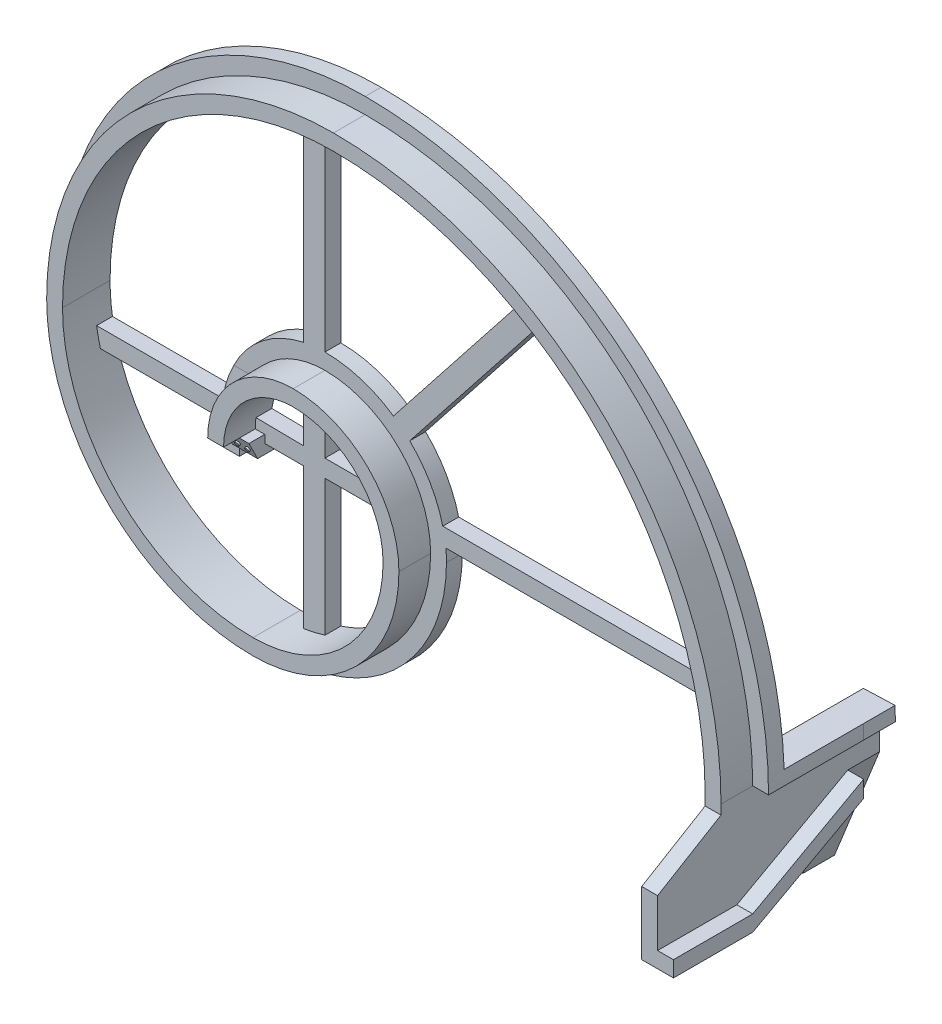
SolidWorks part; units mm, degrees
ref_plane "Front" through (0, 0, 0) normal (0, 0, 1) x (1, 0, 0)
ref_plane "Top" through (0, 0, 0) normal (0, 1, 0) x (1, 0, 0)
ref_plane "Right" through (0, 0, 0) normal (1, 0, 0) x (0, 0, -1)
sketch "Sketch2" plane through (0, 0, 0) normal (0, 0, 1) x (1, 0, 0)
  line L0 (-26.9875, 0) -> (-26.9875, -10)
  line L1 (129.9375, -19.05) -> (134.9375, -19.05)
  line L2 (-21.9875, 0) -> (-21.9875, -10)
  line L3 (-26.9875, -10) -> (-21.9875, -10)
  arc A0 (-21.9875, 0) -> (0, 21.9875) centre (0, 0) cw
  arc A1 (0, 21.9875) -> (28.3375, -6.35) centre (0, -6.35) cw
  arc A2 (28.3375, -6.35) -> (-12.7, -47.3875) centre (-12.7, -6.35) cw
  arc A3 (-12.7, -47.3875) -> (-72.7875, 12.7) centre (-12.7, 12.7) cw
  arc A4 (-72.7875, 12.7) -> (12.7, 98.1875) centre (12.7, 12.7) cw
  arc A5 (12.7, 98.1875) -> (129.9375, -19.05) centre (12.7, -19.05) cw
  arc A6 (-26.9875, 0) -> (0, 26.9875) centre (0, 0) cw
  arc A7 (0, 26.9875) -> (33.3375, -6.35) centre (0, -6.35) cw
  arc A8 (33.3375, -6.35) -> (-12.7, -52.3875) centre (-12.7, -6.35) cw
  arc A9 (-12.7, -52.3875) -> (-77.7875, 12.7) centre (-12.7, 12.7) cw
  arc A10 (-77.7875, 12.7) -> (12.7, 103.1875) centre (12.7, 12.7) cw
  arc A11 (12.7, 103.1875) -> (134.9375, -19.05) centre (12.7, -19.05) cw
extrude "Extrude2" add sketch "Sketch2" along normal blind 10
sketch "Sketch3" plane through (0, 0, 0) normal (0, 0, 1) x (1, 0, 0)
  line L0 (-21.9875, 0) -> (-21.9875, -10)
  line L1 (129.9375, -19.05) -> (139.9375, -19.05)
  line L2 (-21.9875, -10) -> (-31.9875, -10)
  line L3 (-31.9875, -10) -> (-31.9875, 0)
  arc A0 (0, 21.9875) -> (-21.9875, 0) centre (0, 0) ccw
  arc A1 (0, 31.9875) -> (-31.9875, 0) centre (0, 0) ccw
  arc A2 (0, 21.9875) -> (28.3375, -6.35) centre (0, -6.35) cw
  arc A3 (0, 31.9875) -> (38.3375, -6.35) centre (0, -6.35) cw
  arc A4 (28.3375, -6.35) -> (-12.7, -47.3875) centre (-12.7, -6.35) cw
  arc A5 (38.3375, -6.35) -> (-12.7, -57.3875) centre (-12.7, -6.35) cw
  arc A6 (-12.7, -47.3875) -> (-72.7875, 12.7) centre (-12.7, 12.7) cw
  arc A7 (-12.7, -57.3875) -> (-82.7875, 12.7) centre (-12.7, 12.7) cw
  arc A8 (-72.7875, 12.7) -> (12.7, 98.1875) centre (12.7, 12.7) cw
  arc A9 (-82.7875, 12.7) -> (12.7, 108.1875) centre (12.7, 12.7) cw
  arc A10 (12.7, 98.1875) -> (129.9375, -19.05) centre (12.7, -19.05) cw
  arc A11 (12.7, 108.1875) -> (139.9375, -19.05) centre (12.7, -19.05) cw
extrude "Extrude3" add sketch "Sketch3" against normal blind 5
sketch "Sketch4" plane through (-26.9875, 0, 0) normal (-1, 0, 0) x (0, 0, 1)
  line L0 (0, -10) -> (5, 0)
  line L1 (10, -10) -> (0, -10) construction
  line L4 (10, 0) -> (-5, 0) construction
  line L5 (10, -10) -> (0, -10)
  line L6 (5, 0) -> (10, 0)
  line L7 (10, 0) -> (10, -10)
extrude "Cut-Extrude1" cut sketch "Sketch4" against normal blind 5
sketch "Sketch5" plane through (-21.9875, 0, 0) normal (1, 0, 0) x (0, 0, -1)
  line L0 (0, -10) -> (-5, 0)
  line L1 (-5, 0) -> (0, 0)
  line L2 (0, -10) -> (5, -10)
  line L3 (5, -10) -> (5, 0)
  line L4 (5, 0) -> (0, 0)
extrude "Extrude4" add sketch "Sketch5" along normal blind 3
sketch "Sketch6" plane through (-18.9875, 0, 0) normal (1, 0, 0) x (0, 0, -1)
  line L0 (5, -5.5) -> (-2.25, -5.5)
  line L1 (5, -19.05) -> (5, 108.1875) construction
  line L2 (-5, 0) -> (0, -10) construction
  line L3 (-2.25, -5.5) -> (0, -10)
  line L4 (0, -10) -> (5, -10)
  line L5 (5, -10) -> (5, -5.5)
extrude "Cut-Extrude2" cut sketch "Sketch6" against normal blind 8
sketch "Sketch7" plane through (-26.9875, 0, 0) normal (-1, 0, 0) x (0, 0, 1)
  line L0 (0, -5.5) -> (0.7981, -5.5)
  line L1 (0.7981, -5.5) -> (0, 14)
  line L2 (0, 14) -> (0, -5.5)
extrude "Extrude5" add sketch "Sketch7" along normal blind 5 and the other way blind 5
sketch "Sketch8" plane through (0, 0, 0) normal (0, 0, 1) x (1, 0, 0)
  line L0 (-28.7611, 14) -> (-31.9875, 14)
  line L1 (-31.9875, 14) -> (-31.9875, 0)
  arc A0 (-31.9875, 0) -> (-28.7611, 14) centre (0, 0) cw
extrude "Cut-Extrude3" cut sketch "Sketch8" along normal blind 5
sketch "Sketch9" plane through (0, -19.05, 0) normal (0, -1, 0) x (1, 0, 0)
  line L0 (129.9375, 10) -> (129.9375, -5)
  line L1 (129.9375, -5) -> (134.9375, -5)
  line L2 (129.9375, -5) -> (139.9375, -5) construction
  line L3 (134.9375, -5) -> (134.9375, 10)
  line L4 (134.9375, 10) -> (129.9375, 10)
extrude "Extrude6" add sketch "Sketch9" along normal blind 35
sketch "Sketch11" plane through (0, 0, -5) normal (0, 0, -1) x (-1, 0, 0)
  line L0 (-134.9375, -19.05) -> (-129.9375, -19.05)
  line L1 (-129.9375, -19.05) -> (-129.9375, -54.05)
  line L2 (-129.9375, -54.05) -> (-134.9375, -54.05)
  line L3 (-134.9375, -54.05) -> (-134.9375, -19.05)
extrude "Extrude8" add sketch "Sketch11" along normal blind 25
sketch "Sketch12" plane through (0, 0, -5) normal (0, 0, -1) x (-1, 0, 0)
  line L0 (-129.9375, -19.05) -> (-139.9375, -19.05)
  line L1 (-129.8661, -14.9585) -> (-139.86, -14.6095)
  arc A0 (-129.9375, -19.05) -> (-129.8661, -14.9585) centre (-12.7, -19.05) cw
  arc A1 (-139.9375, -19.05) -> (-139.86, -14.6095) centre (-12.7, -19.05) cw
extrude "Extrude9" add sketch "Sketch12" along normal blind 25
sketch "Sketch16" plane through (0, 0, 10) normal (0, 0, 1) x (1, 0, 0)
  line L0 (129.9375, -19.05) -> (129.9375, -54.05)
  line L1 (129.9375, -54.05) -> (139.9375, -54.05)
  line L2 (139.9375, -54.05) -> (139.9375, -49.05)
  line L3 (139.9375, -49.05) -> (134.9375, -49.05)
  line L4 (134.9375, -54.05) -> (134.9375, -19.05) construction
  line L5 (134.9375, -49.05) -> (134.9375, -19.05)
  line L6 (134.9375, -19.05) -> (129.9375, -19.05)
extrude "Extrude12" add sketch "Sketch16" along normal blind 20
sketch "Sketch17" plane through (134.9375, 0, 0) normal (1, 0, 0) x (0, 0, -1)
  line L0 (-10, -54.05) -> (-10, -49.05)
  line L1 (-10, -49.05) -> (-5, -49.05)
  line L2 (-5, -49.05) -> (30, -29.7287)
  line L3 (-10, -54.05) -> (-5, -54.05)
  line L4 (30, -54.05) -> (-10, -54.05) construction
  line L5 (-5, -54.05) -> (30, -34.9887)
  line L6 (30, -19.05) -> (30, -54.05) construction
  line L7 (30, -34.9887) -> (30, -29.7287)
extrude "Extrude13" add sketch "Sketch17" along normal blind 5
sketch "Sketch18" plane through (134.9375, 0, 0) normal (1, 0, 0) x (0, 0, -1)
  line L0 (-5, -54.05) -> (30, -34.9887)
  line L1 (30, -34.9887) -> (30, -54.05)
  line L2 (30, -54.05) -> (-5, -54.05)
  line L4 (-30, -49.05) -> (-30, -19.05) construction
  line L6 (-30, -19.05) -> (-30, -34.05)
  line L7 (-30, -19.05) -> (-10, -19.05)
  line L8 (-10, -19.05) -> (-10, -22.05)
  line L9 (-10, -22.05) -> (-30, -34.05)
extrude "Cut-Extrude5" cut sketch "Sketch18" against normal blind 5
sketch "Sketch19" plane through (0, 0, -30) normal (0, 0, -1) x (-1, 0, 0)
  line L0 (-134.9375, -19.05) -> (-134.9375, -29.7287)
  line L1 (-134.9375, -29.7287) -> (-120.74, -65.09)
  line L2 (-120.74, -65.09) -> (-115.74, -65.09)
  line L3 (-115.74, -65.09) -> (-129.9375, -29.7287)
  line L4 (-129.9375, -34.9887) -> (-129.9375, -19.05) construction
  line L5 (-129.9375, -29.7287) -> (-129.8661, -14.9585)
  line L6 (-129.8661, -14.9585) -> (-139.86, -14.6095)
  line L7 (-139.86, -14.6095) -> (-139.9375, -19.05)
  line L8 (-139.9375, -19.05) -> (-134.9375, -19.05)
extrude "Extrude14" add sketch "Sketch19" along normal blind 10
sketch "Sketch20" plane through (0, 0, 0) normal (0, 0, 1) x (1, 0, 0)
  line L0 (128.7609, -2.482) -> (38.1419, -2.482)
  line L1 (0, 31.9875) -> (0, 97.2389)
  line L2 (37.1788, 3.004) -> (127.8445, 3.004)
  line L3 (-6.7456, 31.2682) -> (-6.7456, 95.9465)
  line L4 (-0.0007, 21.9875) -> (-0.0007, 3.004)
  line L5 (-0.0007, 3.004) -> (26.7491, 3.004)
  line L6 (28.0723, -2.482) -> (0.0805, -2.482)
  line L7 (0.0805, -2.482) -> (0.0805, -45.3123)
  line L8 (-6.7456, 20.9272) -> (-6.7456, 3.004)
  line L9 (-6.7456, 3.004) -> (-21.7528, 3.2043)
  line L10 (-21.9875, 0) -> (-18.9875, 0)
  line L11 (-18.9875, 0) -> (-18.9875, -2.482)
  line L12 (-18.9875, -2.482) -> (-6.7456, -2.482)
  line L13 (-6.7456, -2.482) -> (-6.7456, -46.92)
  line L14 (-31.8266, 3.2043) -> (-50.9222, 3.2043)
  line L15 (-31.9875, 0) -> (-31.9875, -2.4841)
  line L16 (-31.9875, -5.5) -> (-31.9875, 0) construction
  line L17 (-50.9222, 3.2043) -> (-72.0324, 3.2043)
  line L18 (-50.9222, -2.4841) -> (-31.9875, -2.4841)
  line L19 (-50.9222, -2.4841) -> (-70.8373, -2.4841)
  line L20 (26.7491, 21.1136) -> (73.9443, 80.9188)
  line L21 (68.1066, 84.2687) -> (21.611, 25.3159)
  arc A0 (-72.0324, 3.2043) -> (-70.8373, -2.4841) centre (-12.7, 12.7) ccw
  arc A1 (-72.7875, 12.7) -> (-12.7, -47.3875) centre (-12.7, 12.7) ccw construction
  arc A2 (21.611, 25.3159) -> (26.7491, 21.1136) centre (0, -6.35) cw
  arc A4 (73.9443, 80.9188) -> (68.1066, 84.2687) centre (12.7, -19.05) ccw
  arc A6 (129.9375, -19.05) -> (12.7, 98.1875) centre (12.7, -19.05) ccw construction
  arc A8 (38.3375, -6.35) -> (0, 31.9875) centre (0, -6.35) ccw construction
  arc A9 (38.1419, -2.482) -> (37.1788, 3.004) centre (0, -6.35) ccw
  arc A10 (128.7609, -2.482) -> (127.8445, 3.004) centre (12.7, -19.05) ccw
  arc A11 (12.7, 98.1875) -> (-72.7875, 12.7) centre (12.7, 12.7) ccw construction
  arc A12 (0, 31.9875) -> (-28.7611, 14) centre (0, 0) ccw construction
  arc A13 (-6.7456, 31.2682) -> (0, 31.9875) centre (0, 0) cw
  arc A14 (-6.7456, 95.9465) -> (0, 97.2389) centre (12.7, 12.7) cw
  arc A15 (-21.9875, 0) -> (-21.7528, 3.2043) centre (0, 0) cw
  arc A16 (-0.0007, 21.9875) -> (-6.7456, 20.9272) centre (0, 0) ccw
  arc A17 (0, 21.9875) -> (-21.9875, 0) centre (0, 0) ccw construction
  arc A18 (28.0723, -2.482) -> (26.7491, 3.004) centre (0, -6.35) ccw
  arc A19 (28.3375, -6.35) -> (0, 21.9875) centre (0, -6.35) ccw construction
  arc A20 (-6.7456, -46.92) -> (0.0805, -45.3123) centre (-12.706, -6.3177) ccw
  arc A21 (-31.8266, 3.2043) -> (-31.9875, 0) centre (0, 0) ccw
  arc A22 (-28.7611, 14) -> (-31.9875, 0) centre (0, 0) ccw construction
extrude "Extrude19" add sketch "Sketch20" against normal blind 5
sketch "Sketch21" plane through (0, -2, 4) normal (0, -0.4472, 0.8944) x (1, 0, 0)
  circle A0 centre (-23.8075, -1) radius 0.7
  circle A1 centre (-20.6275, -1) radius 0.7
extrude "Extrude20" add sketch "Sketch21" along normal blind 0.5
